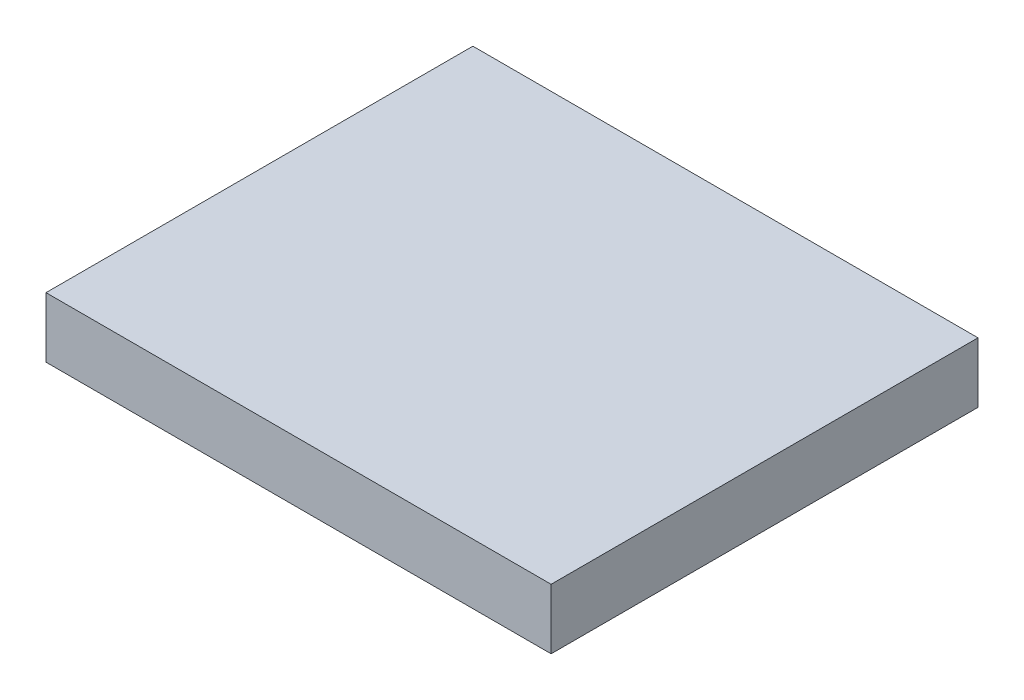
SolidWorks part; units mm, degrees
ref_plane "Front Plane" through (0, 0, 0) normal (0, 0, 1) x (1, 0, 0)
ref_plane "Top Plane" through (0, 0, 0) normal (0, 1, 0) x (1, 0, 0)
ref_plane "Right Plane" through (0, 0, 0) normal (1, 0, 0) x (0, 0, -1)
sketch "Sketch1" plane through (-6.9491, -0.0006, -100.4741) normal (1, 0, 0) x (0, 0, -1)
  line L1 (-687.6215, 163.404) -> (468.5046, 163.404)
  line L2 (-687.6215, 163.404) -> (-687.6215, 326.5259)
  line L3 (-687.6215, 326.5259) -> (468.5046, 326.5259)
  line L4 (468.5046, 163.404) -> (468.5046, 326.5259)
extrude "Boss-Extrude1" add sketch "Sketch1" along normal blind 776 and the other way blind 592
